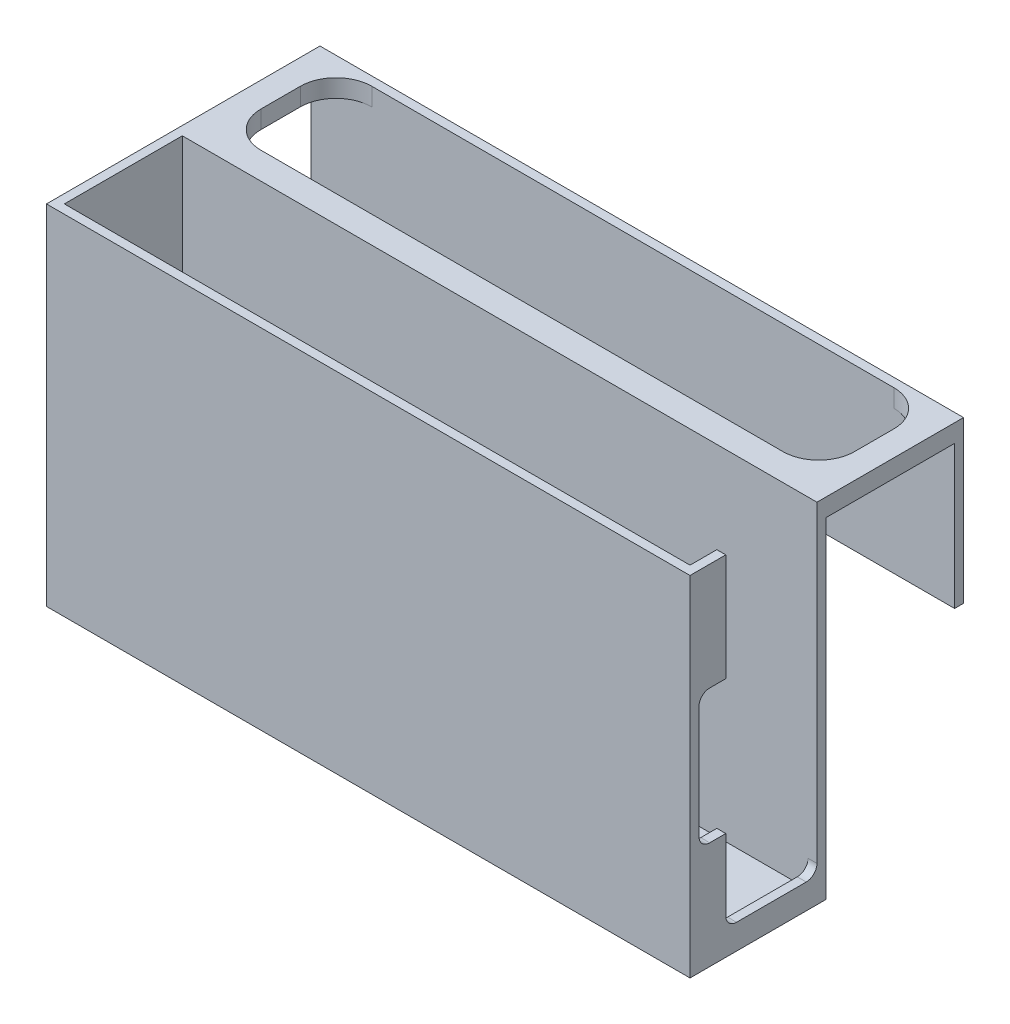
SolidWorks part; units mm, degrees
ref_plane "Piano frontale" through (0, 0, 0) normal (0, 0, 1) x (1, 0, 0)
ref_plane "Piano superiore" through (0, 0, 0) normal (0, 1, 0) x (1, 0, 0)
ref_plane "Piano destro" through (0, 0, 0) normal (1, 0, 0) x (0, 0, -1)
sketch "Sketch1" plane through (0, 0, 0) normal (0, 0, 1) x (1, 0, 0)
  line L0 (-90, 48.75) -> (90, -48.75) construction
  line L1 (-90, 48.75) -> (90, 48.75)
  line L2 (-90, 48.75) -> (-90, -48.75)
  line L3 (-90, -48.75) -> (90, -48.75)
  line L4 (90, 48.75) -> (90, -48.75)
  point P4 (0, 0)
  dimension "D1" = 180
  dimension "D2" = 97.5
extrude "Boss-Extrude1" add sketch "Sketch1" along normal blind 2.5
sketch "Sketch2" plane through (0, 0, 0) normal (0, 0, -1) x (-1, 0, 0)
  line L1 (-90, 48.75) -> (90, 48.75)
  line L2 (-90, 48.75) -> (-90, -48.75)
  line L3 (-90, -48.75) -> (90, -48.75)
  line L4 (90, 48.75) -> (90, -48.75)
  line L5 (-87.5, 46.25) -> (87.5, 46.25)
  line L6 (-87.5, 46.25) -> (-87.5, -46.25)
  line L7 (-87.5, -46.25) -> (87.5, -46.25)
  line L8 (87.5, 46.25) -> (87.5, -46.25)
  dimension "D1" = 2.5
  dimension "D2" = 2.5
  dimension "D3" = 2.5
  dimension "D4" = 2.5
extrude "Boss-Extrude2" add sketch "Sketch2" along normal blind 33
sketch "Sketch3" plane through (0, 0, -33) normal (0, 0, -1) x (-1, 0, 0)
  line L1 (-90, 48.75) -> (90, 48.75)
  line L2 (-90, 48.75) -> (-90, -48.75)
  line L3 (-90, -48.75) -> (90, -48.75)
  line L4 (90, 48.75) -> (90, -48.75)
extrude "Boss-Extrude3" add sketch "Sketch3" along normal blind 2.5
sketch "Sketch4" plane through (0, 0, -35.5) normal (0, 0, -1) x (-1, 0, 0)
  line L0 (90, -48.75) -> (90, 48.75) construction
  line L1 (-90, 48.75) -> (90, 48.75)
  line L2 (-90, 48.75) -> (-90, 43.75)
  line L3 (-90, 43.75) -> (90, 43.75)
  line L4 (90, 48.75) -> (90, 43.75)
  dimension "D1" = 5
extrude "Boss-Extrude4" add sketch "Sketch4" along normal blind 38.5
sketch "Sketch5" plane through (0, 43.75, 0) normal (0, -1, 0) x (1, 0, 0)
  line L0 (90, -74) -> (90, -35.5) construction
  line L1 (-90, -74) -> (90, -74)
  line L2 (-90, -74) -> (-90, -71.5)
  line L3 (-90, -71.5) -> (90, -71.5)
  line L4 (90, -74) -> (90, -71.5)
  dimension "D1" = 2.5
extrude "Boss-Extrude5" add sketch "Sketch5" along normal blind 40
sketch "Sketch7" plane through (0, 48.75, 0) normal (0, 1, 0) x (1, 0, 0)
  line L0 (-90, -2.5) -> (-90, 74) construction
  line L1 (-87.5, 0) -> (87.5, 0)
  line L2 (-87.5, 0) -> (-87.5, 33)
  line L3 (-87.5, 33) -> (87.5, 33)
  line L4 (87.5, 0) -> (87.5, 33)
  line L5 (90, -2.5) -> (-90, -2.5) construction
  line L6 (90, -2.5) -> (90, 74) construction
  dimension "D1" = 2.5
  dimension "D2" = 2.5
  dimension "D3" = 2.5
  dimension "D4" = 33
extrude "Cut-Extrude2" cut sketch "Sketch7" against normal blind 2.5
ref_plane "Plane1" through (87.5, -46.25, -33) normal (0, -1, 0) x (-1, 0, 0)
sketch "Sketch9" plane through (90, 0, 0) normal (1, 0, 0) x (0, 0, -1)
  line L0 (-2.5, -48.75) -> (-2.5, 48.75) construction
  line L1 (33, 48.75) -> (7.5, 48.75)
  line L2 (33, 48.75) -> (33, -38.75)
  line L3 (30, -41.75) -> (10.5, -41.75)
  line L4 (7.5, 48.75) -> (7.5, 18.75)
  line L5 (35.5, 43.75) -> (35.5, -48.75) construction
  line L7 (-2.5, 48.75) -> (74, 48.75) construction
  line L8 (-2.5, -48.75) -> (35.5, -48.75) construction
  line L9 (7.5, -18.75) -> (7.5, -38.75)
  line L10 (3, 18.75) -> (7.5, 18.75)
  line L11 (0, 15.75) -> (0, -15.75)
  line L12 (3, -18.75) -> (7.5, -18.75)
  arc A0 (33, -38.75) -> (30, -41.75) centre (30, -38.75) cw
  arc A1 (10.5, -41.75) -> (7.5, -38.75) centre (10.5, -38.75) cw
  arc A2 (0, -15.75) -> (3, -18.75) centre (3, -15.75) ccw
  arc A3 (3, 18.75) -> (0, 15.75) centre (3, 15.75) ccw
  dimension "D6" = 3
  dimension "D1" = 10
  dimension "D2" = 2.5
  dimension "D3" = 7
  dimension "D4" = 2.5
  dimension "D5" = 30
  dimension "D7" = 23
extrude "Cut-Extrude3" cut sketch "Sketch9" against normal blind 2.5
sketch "Sketch12" plane through (0, 48.75, 0) normal (0, 1, 0) x (1, 0, 0)
  line L0 (90, 33) -> (-87.5, 33) construction
  line L1 (-83, 71.5) -> (83, 71.5)
  line L2 (-83, 71.5) -> (-83, 40.5)
  line L3 (-83, 40.5) -> (83, 40.5)
  line L4 (83, 71.5) -> (83, 40.5)
  line L5 (-90, 74) -> (90, 74) construction
  line L6 (-90, -2.5) -> (-90, 74) construction
  line L7 (90, 33) -> (90, 74) construction
  dimension "D1" = 7.5
  dimension "D2" = 2.5
  dimension "D3" = 7
  dimension "D4" = 7
extrude "Cut-Extrude5" cut sketch "Sketch12" against normal blind 5
fillet "Fillet1" radius 10 1 edges at (83, 46.25, -40.5)
fillet "Fillet2" radius 10 1 edges at (83, 46.25, -71.5)
fillet "Fillet3" radius 10 1 edges at (-83, 46.25, -40.5)
fillet "Fillet4" radius 10 1 edges at (-83, 46.25, -71.5)
